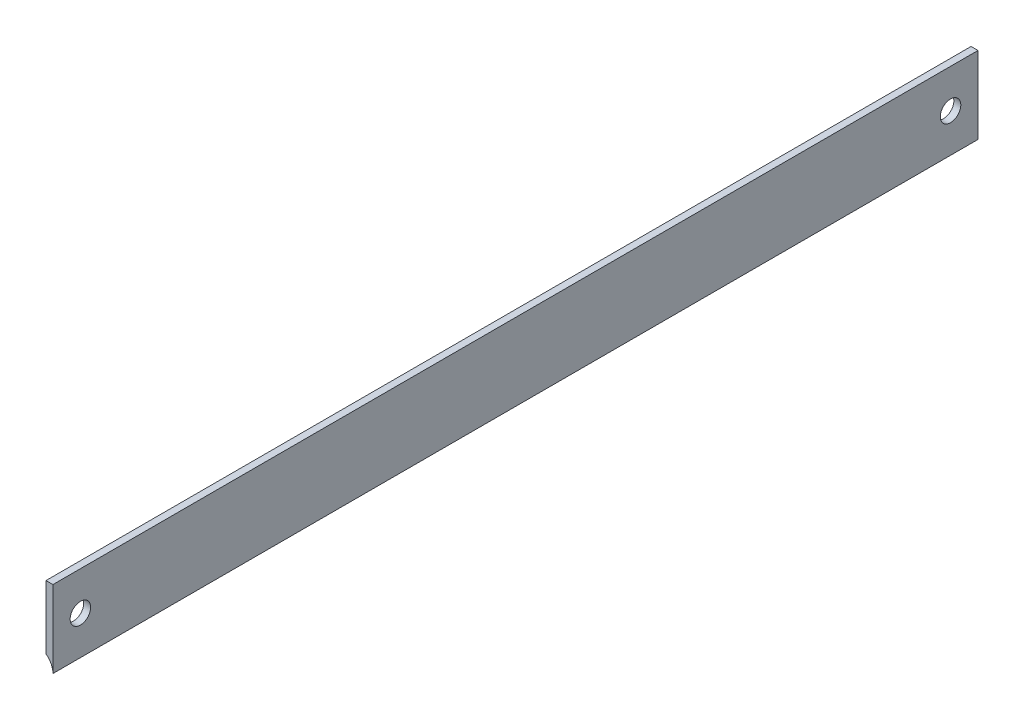
SolidWorks part; units mm, degrees
material "6061-T6 (SS)"
ref_plane "Front Plane" through (0, 0, 0) normal (0, 0, 1) x (1, 0, 0)
ref_plane "Top Plane" through (0, 0, 0) normal (0, 1, 0) x (1, 0, 0)
ref_plane "Right Plane" through (0, 0, 0) normal (1, 0, 0) x (0, 0, -1)
sketch "Sketch1" plane through (0, 0, 0) normal (0, 0, 1) x (1, 0, 0)
  line L2 (-1.143, -8.2568) -> (-1.143, 12.7)
  line L3 (-1.143, 12.7) -> (1.143, 12.7)
  line L4 (1.143, -12.7) -> (1.143, 12.7)
  line L5 (-0.7694, -8.5491) -> (1.143, 12.7) construction
  line L6 (-1.143, 12.7) -> (1.143, -12.7) construction
  arc A0 (1.143, -12.7) -> (-1.143, -8.2568) centre (-4.318, -12.7) ccw
  point P0 (0, 0)
  dimension "D1" = 2.286
  dimension "D3" = 10.922
  dimension "D2" = 25.4
extrude "Boss-Extrude2" add sketch "Sketch1" along normal blind 304.8
sketch "Sketch4" plane through (-1.143, 0, 0) normal (-1, 0, 0) x (0, 0, 1)
  line L0 (0, 0) -> (38.1, 0) construction
  line L1 (0, 12.7) -> (0, -8.2568) construction
  line L2 (304.8, 12.7) -> (304.8, -8.2568) construction
  line L3 (304.8, 12.7) -> (0, 12.7) construction
  point P6 (9.05, 0)
  point P7 (295.75, 0)
  dimension "D1" = 9.05
  dimension "D2" = 9.05
  dimension "D3" = 12.7
hole_wizard "1/4 Clearance Hole2" positions "Sketch6" profile "Sketch5" hole size "1/4" standard "ANSI Inch" end condition through all
sketch "Sketch6" plane through (-1.143, 0, 0) normal (-1, 0, 0) x (0, 0, 1)
  point P0 (9.05, 0)
  point P3 (295.75, 0)
sketch "Sketch5" plane through (-1.143, 0, 9.05) normal (0, 1, 0) x (0, 0, 1)
  line L0 (0, 0) -> (0, 2.286)
  line L1 (0, 2.286) -> (3.3782, 2.286)
  line L2 (3.3782, 2.286) -> (3.3782, 0)
  line L5 (3.3782, 0) -> (0, 0)
  line L11 (0, -6.35) -> (0, 107.95) construction
  dimension "Thru Hole Dia." = 6.7564
  dimension "Thru Hole Depth" = 2.286
